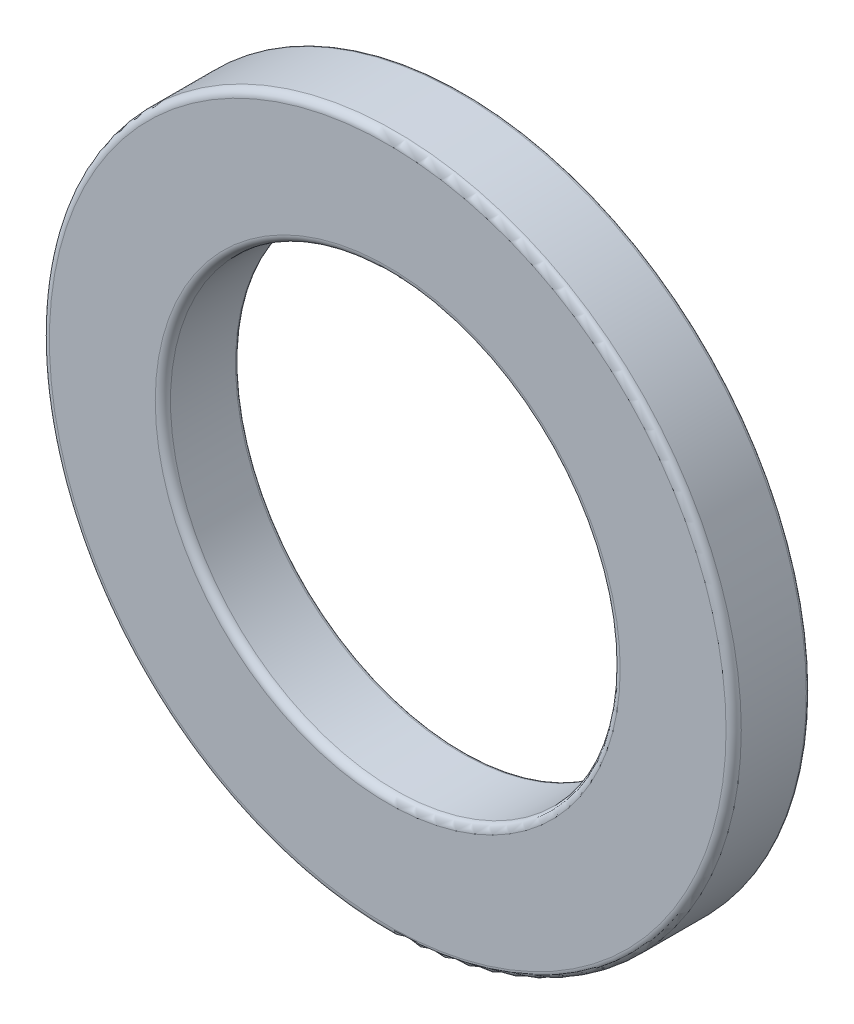
SolidWorks part; units mm, degrees
ref_plane "Front Plane" through (0, 0, 0) normal (0, 0, 1) x (1, 0, 0)
ref_plane "Top Plane" through (0, 0, 0) normal (0, 1, 0) x (1, 0, 0)
ref_plane "Right Plane" through (0, 0, 0) normal (1, 0, 0) x (0, 0, -1)
sketch "Sketch1" plane through (0, 0, 0) normal (0, 0, 1) x (1, 0, 0)
  circle A0 centre (0, 0) radius 10 construction
  circle A1 centre (0, 0) radius 6.5 construction
  point P5 (0, -10)
  dimension "OD" = 20
  dimension "ID" = 13
sketch "Sketch2" plane through (0, 0, 0) normal (1, 0, 0) x (0, 0, -1)
  line L0 (0.9, 0) -> (-0.9, 0) construction
  line L1 (-1.1, -10) -> (1.1, -10) construction
  point P0 (-1.1, -10)
  point P3 (1.1, -10)
  point P4 (0, 0)
  point P9 (0, -10)
  point P10 (0.9, -10)
  point P11 (-1.1, -10)
  point P12 (-0.9, -10)
  point P13 (1.1, -10)
  dimension "Thickness Range [Min]" = 1.8
  dimension "Thickness Range [Max]" = 2.2
sketch "Sketch3" plane through (0, 0, 0) normal (0, 0, 1) x (1, 0, 0)
  circle A0 centre (0, 0) radius 6.5 construction
  circle A1 centre (0, 0) radius 10 construction
  circle A2 centre (0, 0) radius 6.5
  circle A3 centre (0, 0) radius 10
extrude "Boss-Extrude1" add sketch "Sketch3" against normal up to vertex (1.1 mm away) and the other way up to vertex (1.1 mm away) up to point (0, -10, -1.1) other way up to point (0, -10, 1.1)
fillet "Fillet1" radius 0.22 2 edges at (6.5, 0, 1.1) (10, 0, 1.1)
fillet "Fillet2" radius 0.1 2 edges at (10, 0, -1.1) (6.5, 0, -1.1)
equation "\"D1@Fillet2\"=\"OD@Sketch1\"*.005"
